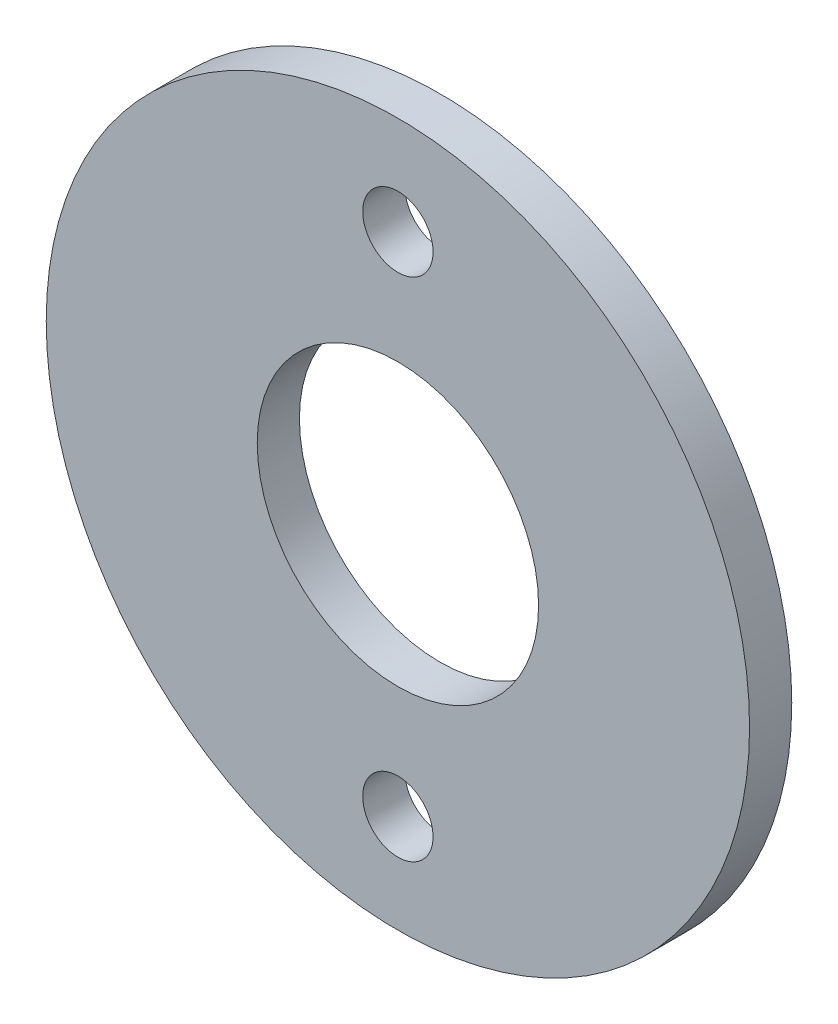
SolidWorks part; units mm, degrees
ref_plane "Alzado" through (0, 0, 0) normal (0, 0, 1) x (1, 0, 0)
ref_plane "Planta" through (0, 0, 0) normal (0, 1, 0) x (1, 0, 0)
ref_plane "Vista lateral" through (0, 0, 0) normal (1, 0, 0) x (0, 0, -1)
sketch "Croquis1" plane through (0, 0, 0) normal (0, 0, 1) x (1, 0, 0)
  line L0 (0, 0) -> (0, 12) construction
  line L1 (0, 0) -> (26.972, 0) construction
  circle A0 centre (0, 0) radius 5
  circle A1 centre (0, 0) radius 12.5
  dimension "D1" = 25
  dimension "D2" = 10
extrude "Saliente-Extruir1" add sketch "Croquis1" along normal blind 1.5
sketch "Croquis2" plane through (0, 0, 1.5) normal (0, 0, 1) x (1, 0, 0)
  line L0 (0, 0) -> (12.5, 0) construction
  line L1 (0, 0) -> (0, 5) construction
  line L2 (0, 5) -> (0, 12.5) construction
  line L3 (0, 0) -> (0, 7) construction
  line L4 (0, 7) -> (0, 9) construction
  circle A0 centre (0, 0) radius 12.5 construction
  circle A1 centre (0, 0) radius 5 construction
  circle A2 centre (0, 9) radius 1.25
  circle A3 centre (0, -9) radius 1.25
extrude "Cortar-Extruir1" cut sketch "Croquis2" against normal through all
